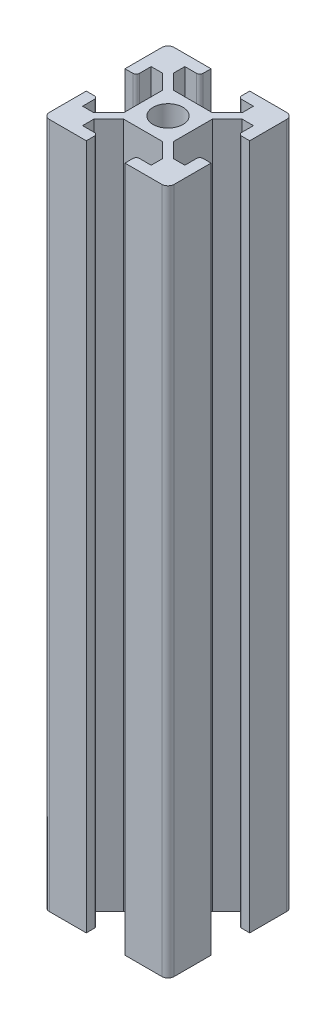
SolidWorks part; units mm, degrees
material "6063-T1"
ref_plane "Front Plane" through (0, 0, 0) normal (0, 0, 1) x (1, 0, 0)
ref_plane "Top Plane" through (0, 0, 0) normal (0, 1, 0) x (1, 0, 0)
ref_plane "Right Plane" through (0, 0, 0) normal (1, 0, 0) x (0, 0, -1)
sketch "Sketch1" plane through (0, 0, 0) normal (0, 1, 0) x (1, 0, 0)
  line L0 (0, 14.3976) -> (0, -18.4644) construction
  line L1 (-9, -10) -> (9, -10)
  line L2 (-10, -9) -> (-10, 9)
  line L3 (-9, 10) -> (9, 10)
  line L4 (10, -9) -> (10, 9)
  line L5 (-15.9976, 0) -> (13.6764, 0) construction
  line L6 (3.1, 10) -> (3.1, 8.2) construction
  line L7 (3.1, 8.2) -> (5.5, 8.2) construction
  line L8 (8.2, 5.5) -> (6.3765, 5.5) construction
  line L9 (3.1235, 4) -> (0, 4) construction
  line L10 (10, 3.1) -> (8.2, 3.1) construction
  line L11 (8.2, 3.1) -> (8.2, 5.5) construction
  line L12 (5.5, 8.2) -> (5.5, 6.3765) construction
  line L13 (4, 3.1235) -> (4, 0) construction
  line L14 (6.3765, 5.5) -> (4, 3.1235) construction
  line L15 (3.1, 10) -> (3.1, 8.7)
  line L16 (5.5, 6.3765) -> (3.1235, 4) construction
  line L17 (3.6, 8.2) -> (5.5, 8.2)
  line L18 (5.5, 8.2) -> (5.5, 6.3765)
  line L19 (5.5, 6.3765) -> (3.1235, 4)
  line L20 (3.1235, 4) -> (0, 4)
  line L21 (10, 3.1) -> (8.7, 3.1)
  line L22 (8.2, 3.6) -> (8.2, 5.5)
  line L23 (8.2, 5.5) -> (6.3765, 5.5)
  line L24 (6.3765, 5.5) -> (4, 3.1235)
  line L25 (4, 3.1235) -> (4, 0)
  line L26 (3.1, 10) -> (9, 10)
  line L27 (8.2, -5.5) -> (6.3765, -5.5)
  line L28 (8.2, -3.6) -> (8.2, -5.5)
  line L29 (10, -3.1) -> (8.7, -3.1)
  line L30 (6.3765, -5.5) -> (4, -3.1235)
  line L31 (4, -3.1235) -> (4, 0)
  line L32 (5.5, -6.3765) -> (3.1235, -4)
  line L33 (3.1235, -4) -> (0, -4)
  line L34 (5.5, -8.2) -> (5.5, -6.3765)
  line L35 (3.6, -8.2) -> (5.5, -8.2)
  line L36 (3.1, -10) -> (3.1, -8.7)
  line L37 (-5.5, -8.2) -> (-5.5, -6.3765)
  line L38 (-3.6, -8.2) -> (-5.5, -8.2)
  line L39 (-3.1, -10) -> (-3.1, -8.7)
  line L40 (-5.5, -6.3765) -> (-3.1235, -4)
  line L41 (-3.1235, -4) -> (0, -4)
  line L42 (-6.3765, -5.5) -> (-4, -3.1235)
  line L43 (-4, -3.1235) -> (-4, 0)
  line L44 (-8.2, -5.5) -> (-6.3765, -5.5)
  line L45 (-8.2, -3.6) -> (-8.2, -5.5)
  line L46 (-10, -3.1) -> (-8.7, -3.1)
  line L47 (-8.2, 5.5) -> (-6.3765, 5.5)
  line L48 (-8.2, 3.6) -> (-8.2, 5.5)
  line L49 (-10, 3.1) -> (-8.7, 3.1)
  line L50 (-6.3765, 5.5) -> (-4, 3.1235)
  line L51 (-4, 3.1235) -> (-4, 0)
  line L52 (-5.5, 6.3765) -> (-3.1235, 4)
  line L53 (-3.1235, 4) -> (0, 4)
  line L54 (-5.5, 8.2) -> (-5.5, 6.3765)
  line L55 (-3.6, 8.2) -> (-5.5, 8.2)
  line L56 (-3.1, 10) -> (-3.1, 8.7)
  circle A0 centre (0, 0) radius 2.4
  arc A1 (9, 10) -> (10, 9) centre (9, 9) cw
  arc A2 (9, -10) -> (10, -9) centre (9, -9) ccw
  arc A3 (-9, -10) -> (-10, -9) centre (-9, -9) cw
  arc A4 (-10, 9) -> (-9, 10) centre (-9, 9) cw
  arc A5 (8.7, 3.1) -> (8.2, 3.6) centre (8.7, 3.6) cw
  arc A6 (3.1, 8.7) -> (3.6, 8.2) centre (3.6, 8.7) ccw
  arc A7 (8.7, -3.1) -> (8.2, -3.6) centre (8.7, -3.6) ccw
  arc A8 (3.1, -8.7) -> (3.6, -8.2) centre (3.6, -8.7) cw
  arc A9 (-3.1, -8.7) -> (-3.6, -8.2) centre (-3.6, -8.7) ccw
  arc A10 (-8.7, -3.1) -> (-8.2, -3.6) centre (-8.7, -3.6) cw
  arc A11 (-8.7, 3.1) -> (-8.2, 3.6) centre (-8.7, 3.6) ccw
  arc A12 (-3.1, 8.7) -> (-3.6, 8.2) centre (-3.6, 8.7) cw
  point P0 (0, 0)
  point P10 (10, 10)
  point P13 (10, -10)
  point P18 (-10, 10)
  point P92 (0, 0)
  dimension "D5" = 4.8
  dimension "D6" = 1
  dimension "D17" = 0.5
  dimension "D1" = 20
  dimension "D2" = 20
  dimension "D3" = 10
  dimension "D4" = 10
  dimension "D7" = 1.8
  dimension "D8" = 1.8
  dimension "D9" = 3.1
  dimension "D10" = 3.1
  dimension "D11" = 5.5
  dimension "D12" = 4
  dimension "D13" = 5.5
  dimension "D14" = 4
  dimension "D15" = 4.2
  dimension "D16" = 45
  dimension "D18" = 3.1235
  dimension "D19" = 4
extrude "Boss-Extrude1" add sketch "Sketch1" along normal blind 110 contours A12 L56 L3 A4 L2 L49 A11 L48 L47 L50 L51 L43 L42 L44 L45 A10 L46 A3 L1 L39 A9 L38 L37 L40 L41 L33 L32 L34 L35 A8 L36 A2 L4 L29 A7 L28 L27 L30 L31 L25 L24 L23 L22 A5 L21 A1 L15
